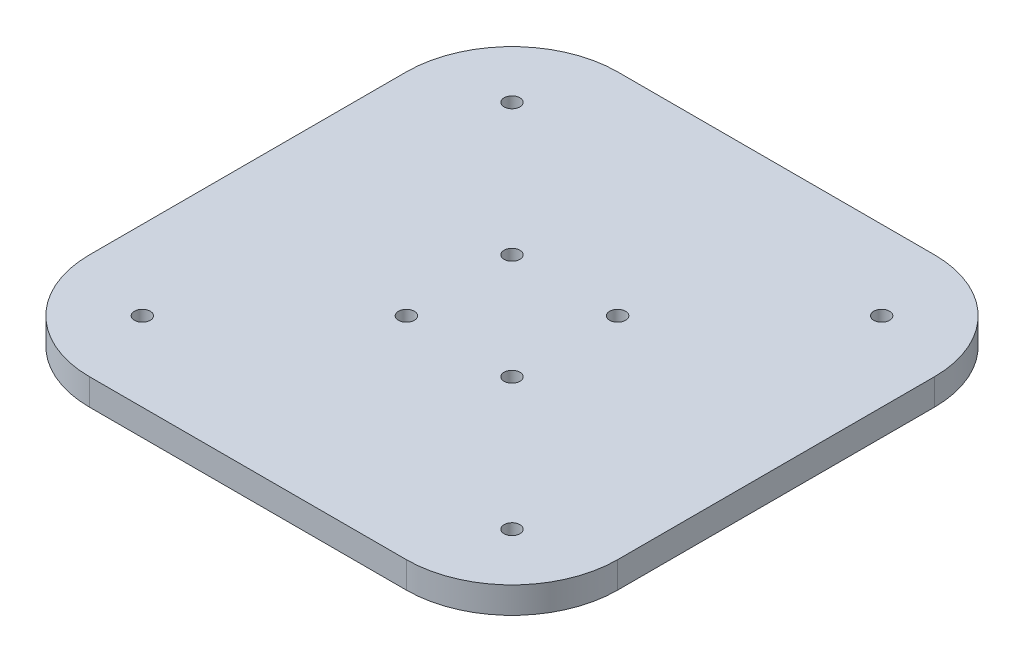
SolidWorks part; units mm, degrees
ref_plane "前视基准面" through (0, 0, 0) normal (0, 0, 1) x (1, 0, 0)
ref_plane "上视基准面" through (0, 0, 0) normal (0, 1, 0) x (1, 0, 0)
ref_plane "右视基准面" through (0, 0, 0) normal (1, 0, 0) x (0, 0, -1)
sketch "草图1" plane through (0, 0, 0) normal (0, 1, 0) x (1, 0, 0)
  line L0 (0, 50) -> (0, -50) construction
  line L1 (50, -50) -> (-50, -50)
  line L2 (50, -50) -> (50, 50)
  line L3 (50, 50) -> (-50, 50)
  line L4 (-50, -50) -> (-50, 50)
  line L5 (50, -50) -> (-50, 50) construction
  line L6 (50, 50) -> (-50, -50) construction
  line L7 (0, 0) -> (-20, 35) construction
  line L8 (-50, 0) -> (50, 0) construction
  circle A12 centre (-35, 35) radius 1.5
  circle A14 centre (35, 35) radius 1.5
  circle A16 centre (35, -35) radius 1.5
  circle A18 centre (-35, -35) radius 1.5
  circle A20 centre (-10, 10) radius 1.5
  circle A21 centre (10, 10) radius 1.5
  circle A22 centre (10, -10) radius 1.5
  circle A23 centre (-10, -10) radius 1.5
  point P0 (0, 0)
  dimension "D3" = 3
  dimension "D9" = 3
  dimension "D10" = 15
  dimension "D1" = 100
  dimension "D2" = 100
  dimension "D4" = 10
  dimension "D5" = 10
  dimension "D7" = 15
  dimension "D8" = 15
  dimension "D15" = 40.3113
  dimension "D16" = 47.7534
  dimension "D6" = 15
  dimension "D14" = 4
extrude "凸台-拉伸1" add sketch "草图1" along normal blind 5
fillet "圆角1" radius 20 4 edges at (-50, 2.5, 50) (50, 2.5, 50) (50, 2.5, -50) (-50, 2.5, -50)
